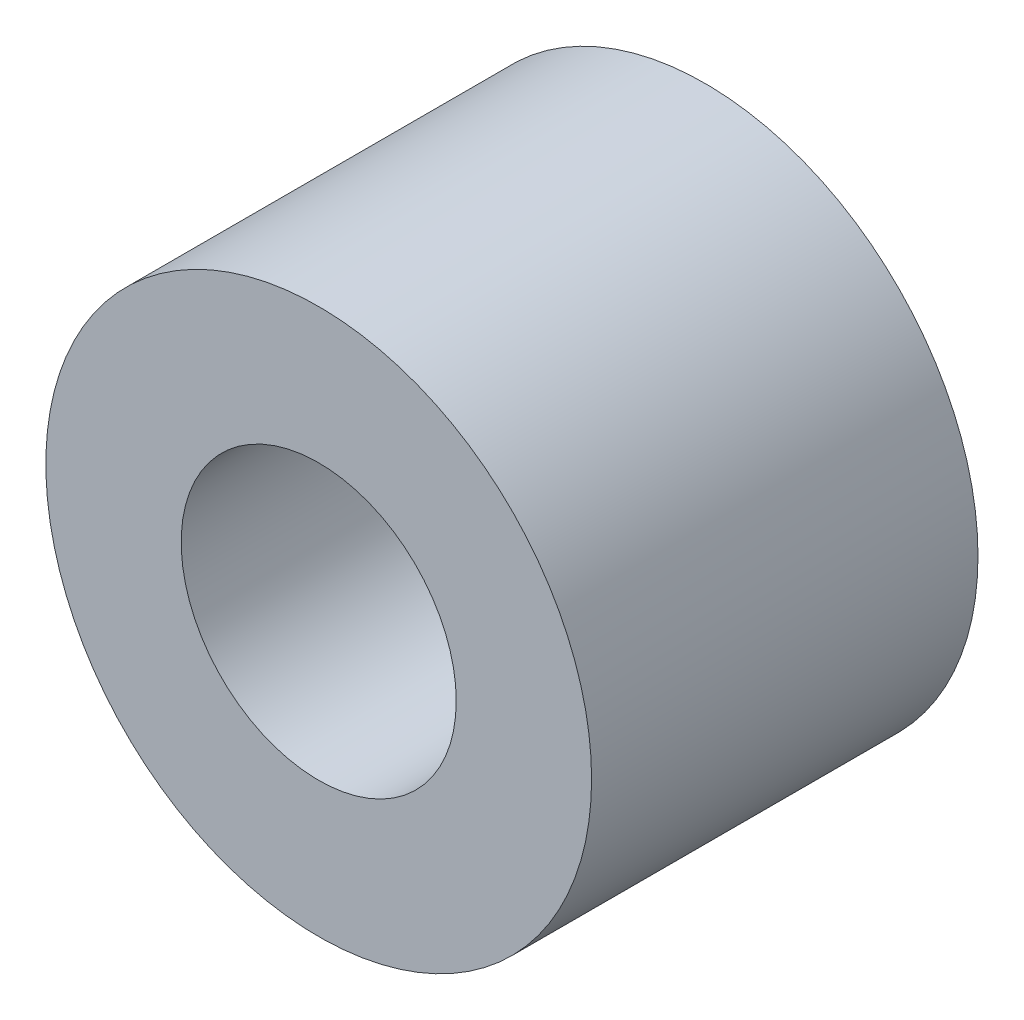
SolidWorks part; units mm, degrees
ref_plane "Front Plane" through (0, 0, 0) normal (0, 0, 1) x (1, 0, 0)
ref_plane "Top Plane" through (0, 0, 0) normal (0, 1, 0) x (1, 0, 0)
ref_plane "Right Plane" through (0, 0, 0) normal (1, 0, 0) x (0, 0, -1)
sketch "Sketch1" plane through (0, 0, 0) normal (0, 0, 1) x (1, 0, 0)
  circle A0 centre (0, 0) radius 3.2004
  circle A1 centre (0, 0) radius 6.35
  dimension "D1" = 6.4008
  dimension "D2" = 12.7
extrude "Boss-Extrude1" add sketch "Sketch1" along normal blind 8.9916
